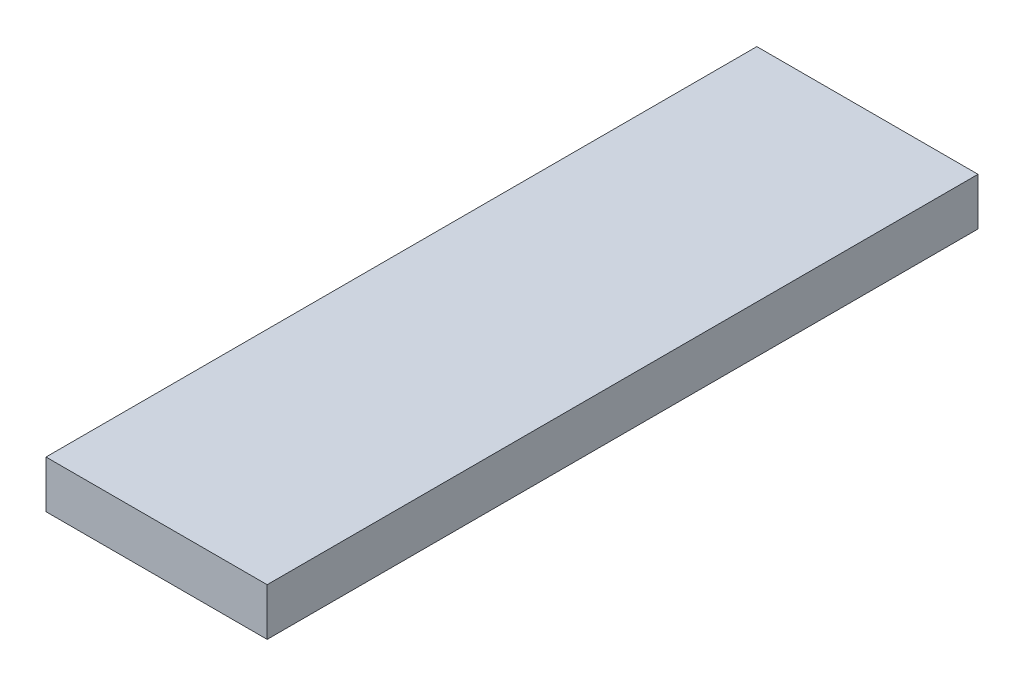
SolidWorks part; units mm, degrees
ref_plane "Plan de face" through (0, 0, 0) normal (0, 0, 1) x (1, 0, 0)
ref_plane "Plan de dessus" through (0, 0, 0) normal (0, 1, 0) x (1, 0, 0)
ref_plane "Plan de droite" through (0, 0, 0) normal (1, 0, 0) x (0, 0, -1)
sketch "Esquisse1" plane through (0, 0, 0) normal (0, 1, 0) x (1, 0, 0)
  line L1 (0, 0) -> (14, 0)
  line L2 (0, 0) -> (0, 45)
  line L3 (0, 45) -> (14, 45)
  line L4 (14, 0) -> (14, 45)
  dimension "D1" = 45
  dimension "D2" = 14
extrude "Boss.-Extru.1" add sketch "Esquisse1" along normal blind 3
